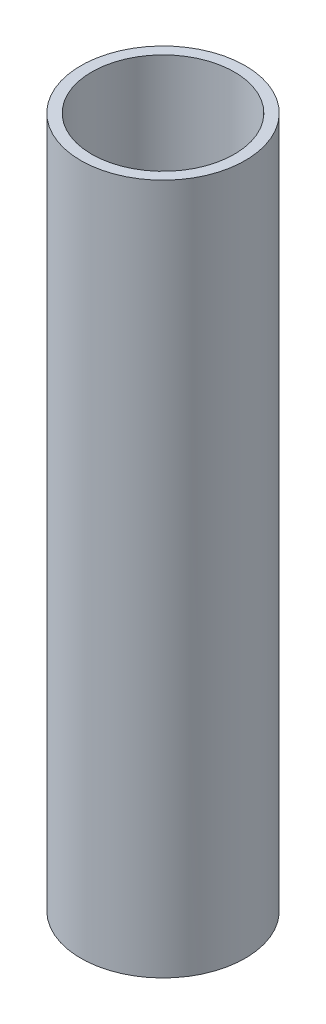
SolidWorks part; units mm, degrees
ref_plane "Front Plane" through (0, 0, 0) normal (0, 0, 1) x (1, 0, 0)
ref_plane "Top Plane" through (0, 0, 0) normal (0, 1, 0) x (1, 0, 0)
ref_plane "Right Plane" through (0, 0, 0) normal (1, 0, 0) x (0, 0, -1)
sketch "Sketch1" plane through (0, 0, 0) normal (0, 1, 0) x (1, 0, 0)
  circle A0 centre (0, 0) radius 12.85
  circle A1 centre (0, 0) radius 11.15
  dimension "D1" = 25.7
  dimension "D2" = 22.3
extrude "Boss-Extrude1" add sketch "Sketch1" along normal blind 102
sketch "Sketch2" plane through (0, 0, 0) normal (0, -1, 0) x (1, 0, 0)
  circle A0 centre (0, 0) radius 12.85
extrude "Boss-Extrude2" add sketch "Sketch2" along normal blind 6
